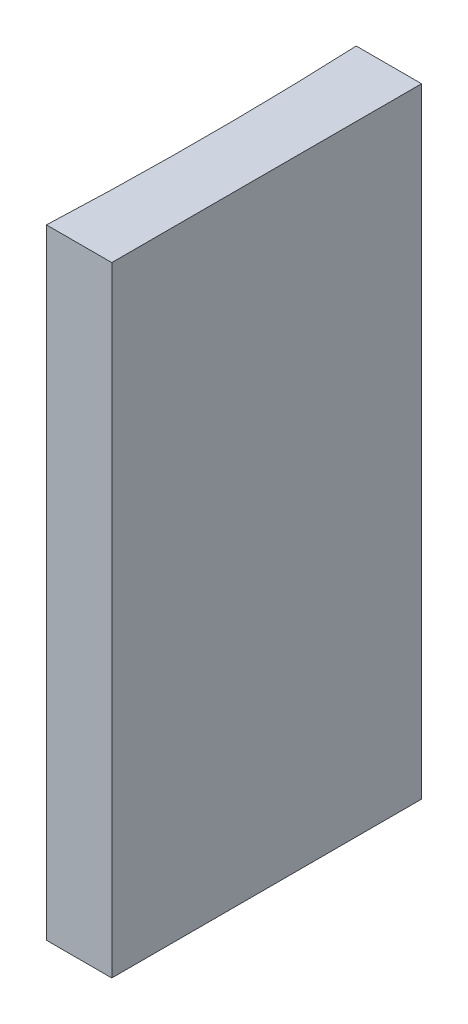
SolidWorks part; units mm, degrees
ref_plane "前视基准面" through (0, 0, 0) normal (0, 0, 1) x (1, 0, 0)
ref_plane "上视基准面" through (0, 0, 0) normal (0, 1, 0) x (1, 0, 0)
ref_plane "右视基准面" through (0, 0, 0) normal (1, 0, 0) x (0, 0, -1)
sketch "草图1" plane through (0, 0, 0) normal (0, 1, 0) x (1, 0, 0)
  line L0 (0, 0) -> (0, -10)
  line L1 (0, 0) -> (-2.1091, 0)
  line L2 (0, -10) -> (-2.1091, -10)
  line L3 (21.2259, -5) -> (-21.2259, -5) construction
  arc A0 (-2.1091, -10) -> (-2.1091, 0) centre (-116.62, -5) ccw
  point P7 (-2, -5)
  point P8 (0, -5)
  dimension "D2" = 114.62
  dimension "D3" = 2
  dimension "D1" = 10
extrude "凸台-拉伸1" add sketch "草图1" along normal blind 20
